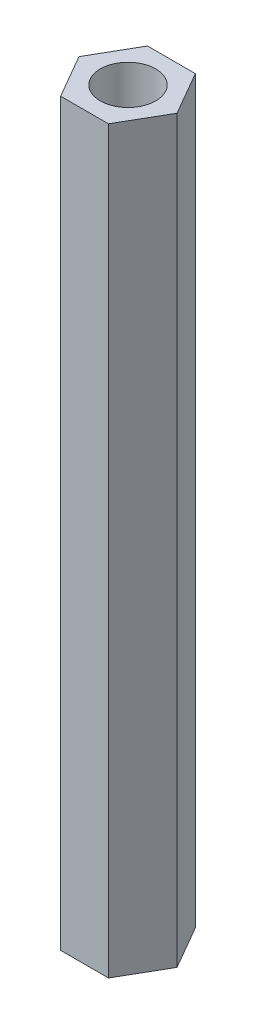
SolidWorks part; units mm, degrees
ref_plane "前视基准面" through (0, 0, 0) normal (0, 0, 1) x (1, 0, 0)
ref_plane "上视基准面" through (0, 0, 0) normal (0, 1, 0) x (1, 0, 0)
ref_plane "右视基准面" through (0, 0, 0) normal (1, 0, 0) x (0, 0, -1)
sketch "草图1" plane through (0, 0, 0) normal (0, 1, 0) x (1, 0, 0)
  line L0 (-12.6472, 0) -> (11.4268, 0) construction
  line L1 (0, 12.1757) -> (0, -13.2296) construction
  line L2 (1.2932, 2.35) -> (-1.2932, 2.35)
  line L7 (1.2932, -2.35) -> (-1.2932, -2.35)
  line L8 (1.2932, 2.35) -> (2.65, 0)
  line L9 (-1.2932, 2.35) -> (-2.65, 0)
  line L10 (1.2932, -2.35) -> (2.65, 0)
  line L11 (-1.2932, -2.35) -> (-2.65, 0)
  circle A0 centre (0, 0) radius 1.5
  point P12 (0, 2.35)
  dimension "D1" = 3
  dimension "D2" = 5.3
  dimension "D3" = 4.7
  dimension "D4" = 120
extrude "凸台-拉伸1" add sketch "草图1" along normal blind 40
